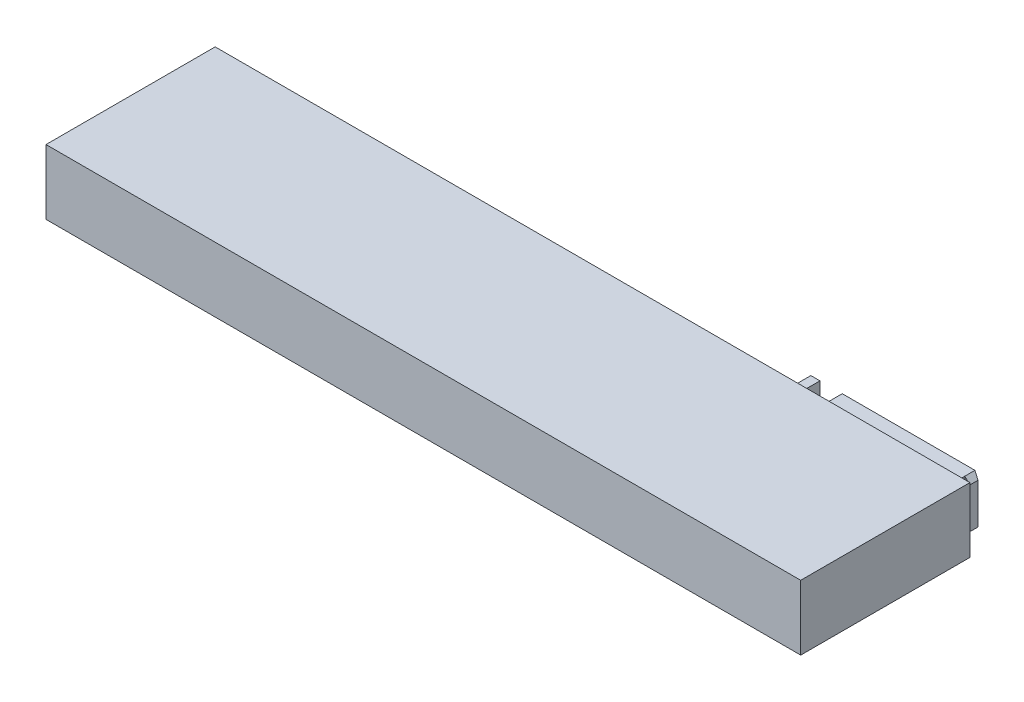
SolidWorks part; units mm, degrees
ref_plane "Front Plane" through (0, 0, 0) normal (0, 0, 1) x (1, 0, 0)
ref_plane "Top Plane" through (0, 0, 0) normal (0, 1, 0) x (1, 0, 0)
ref_plane "Right Plane" through (0, 0, 0) normal (1, 0, 0) x (0, 0, -1)
sketch "Sketch1" plane through (0, 0, 0) normal (0, 1, 0) x (1, 0, 0)
  line L1 (0, 0) -> (-74.5, 0)
  line L2 (0, 0) -> (0, 16.7)
  line L3 (0, 16.7) -> (-74.5, 16.7)
  line L4 (-74.5, 0) -> (-74.5, 16.7)
  dimension "D1" = 74.5
  dimension "D2" = 16.7
extrude "Boss-Extrude1" add sketch "Sketch1" along normal blind 6.4
sketch "Sketch2" plane through (0, 0, -16.7) normal (0, 0, -1) x (-1, 0, 0)
  line L0 (0, 3.2) -> (74.5, 3.2) construction
  line L1 (1.5, 5.7) -> (14.6, 5.7)
  line L2 (1.5, 5.7) -> (1.5, 0.7)
  line L3 (1.5, 0.7) -> (14.6, 0.7)
  line L4 (14.6, 5.7) -> (14.6, 0.7)
  line L5 (1.5, 5.7) -> (14.6, 0.7) construction
  line L6 (1.5, 0.7) -> (14.6, 5.7) construction
  line L7 (0, 6.4) -> (0, 0) construction
  line L8 (74.5, 6.4) -> (74.5, 0) construction
  line L10 (16.8, 5.7) -> (17.7, 5.7)
  line L11 (16.8, 5.7) -> (16.8, 0.7)
  line L12 (16.8, 0.7) -> (17.7, 0.7)
  line L13 (17.7, 5.7) -> (17.7, 0.7)
  line L14 (16.8, 5.7) -> (17.7, 0.7) construction
  line L15 (16.8, 0.7) -> (17.7, 5.7) construction
  point P0 (8.05, 3.2)
  point P12 (17.25, 3.2)
  dimension "D1" = 13.1
  dimension "D2" = 16.2
  dimension "D3" = 2.2
  dimension "D4" = 5
  dimension "D5" = 1.5
extrude "Boss-Extrude2" add sketch "Sketch2" along normal blind 2
sketch "Sketch3" plane through (0, 0, -18.7) normal (0, 0, -1) x (-1, 0, 0)
  line L0 (1.5, 3.2) -> (14.6, 3.2) construction
  line L1 (1.5, 5.7) -> (1.5, 0.7) construction
  line L2 (14.6, 0.7) -> (14.6, 5.7) construction
  line L3 (0, 6.4) -> (0, 0) construction
  line L4 (5.1, 1.95) -> (12.6, 1.95) construction
  line L5 (5.1, 1.95) -> (5.1, 4.45) construction
  line L6 (5.1, 4.45) -> (12.6, 4.45) construction
  line L7 (12.6, 1.95) -> (12.6, 4.45) construction
  line L8 (5.1, 1.95) -> (12.6, 4.45) construction
  line L9 (5.1, 4.45) -> (12.6, 1.95) construction
  circle A0 centre (5.1, 4.45) radius 1.05
  circle A1 centre (7.6, 4.45) radius 1.05
  circle A2 centre (10.1, 4.45) radius 1.05
  circle A3 centre (12.6, 4.45) radius 1.05
  circle A4 centre (12.6, 1.95) radius 1.05
  circle A5 centre (10.1, 1.95) radius 1.05
  circle A6 centre (7.6, 1.95) radius 1.05
  circle A7 centre (5.1, 1.95) radius 1.05
  point P6 (8.85, 3.2)
  dimension "D1" = 2.1
  dimension "D4" = 2.5
  dimension "D5" = 2.5
  dimension "D2" = 2.5
  dimension "D3" = 7.5
  dimension "D6" = 5.1
extrude "Cut-Extrude1" cut sketch "Sketch3" against normal blind 15
sketch "Sketch4" plane through (-1.5, 0, 0) normal (1, 0, 0) x (0, 0, -1)
  line L1 (18.7, 5.7) -> (17.7, 5.7)
  line L2 (18.7, 5.7) -> (18.7, 0.7)
  line L3 (18.7, 0.7) -> (17.7, 0.7)
  line L4 (17.7, 5.7) -> (17.7, 0.7)
  line L5 (18.7, 0.7) -> (16.7, 0.7) construction
extrude "Boss-Extrude3" add sketch "Sketch4" along normal blind 0.5
sketch "Sketch5" plane through (-17.7, 0, 0) normal (-1, 0, 0) x (0, 0, 1)
  line L0 (-18.7, 5.7) -> (-16.7, 5.7) construction
  line L1 (-18.7, 0.7) -> (-17.7, 0.7)
  line L2 (-18.7, 0.7) -> (-18.7, 5.7)
  line L3 (-18.7, 5.7) -> (-17.7, 5.7)
  line L4 (-17.7, 0.7) -> (-17.7, 5.7)
extrude "Boss-Extrude4" add sketch "Sketch5" along normal blind 0.5
chamfer "Chamfer2" distance 0.5 distance2 0.2 2 edges at (-18.2, 3.2, -18.7) (-1, 3.2, -18.7)
chamfer "Chamfer1" distance 0.5 angle 45 4 edges at (-18.2, 0.7, -18.1) (-18.2, 5.7, -18.1) (-1, 5.7, -18.1) (-1, 0.7, -18.1)
sketch "Sketch6" plane through (0, 0, -16.7) normal (0, 0, -1) x (-1, 0, 0)
  line L0 (0, 3.2) -> (74.5, 3.2) construction
  line L1 (0, 6.4) -> (0, 0) construction
  line L2 (74.5, 6.4) -> (74.5, 0) construction
  line L4 (21.5, 5.2) -> (26.5, 5.2)
  line L5 (21.5, 5.2) -> (21.5, 1.2)
  line L6 (21.5, 1.2) -> (26.5, 1.2)
  line L7 (26.5, 5.2) -> (26.5, 1.2)
  line L8 (21.5, 5.2) -> (26.5, 1.2) construction
  line L9 (21.5, 1.2) -> (26.5, 5.2) construction
  point P6 (24, 3.2)
  dimension "D1" = 5
  dimension "D2" = 4
  dimension "D3" = 24
extrude "Boss-Extrude5" add sketch "Sketch6" along normal blind 0.3
sketch "Sketch7" plane through (0, 0, -17) normal (0, 0, -1) x (-1, 0, 0)
  line L0 (21.5, 1.2) -> (26.5, 1.2) construction
  line L1 (21.5, 5.2) -> (21.5, 1.2) construction
  circle A0 centre (24, 3.2) radius 1.25
  point P5 (24, 1.2)
  point P9 (21.5, 3.2)
  dimension "D1" = 2.5
extrude "Boss-Extrude6" add sketch "Sketch7" along normal blind 0.7
equation "\"D1@Boss-Extrude2\"=18.7-16.7"
